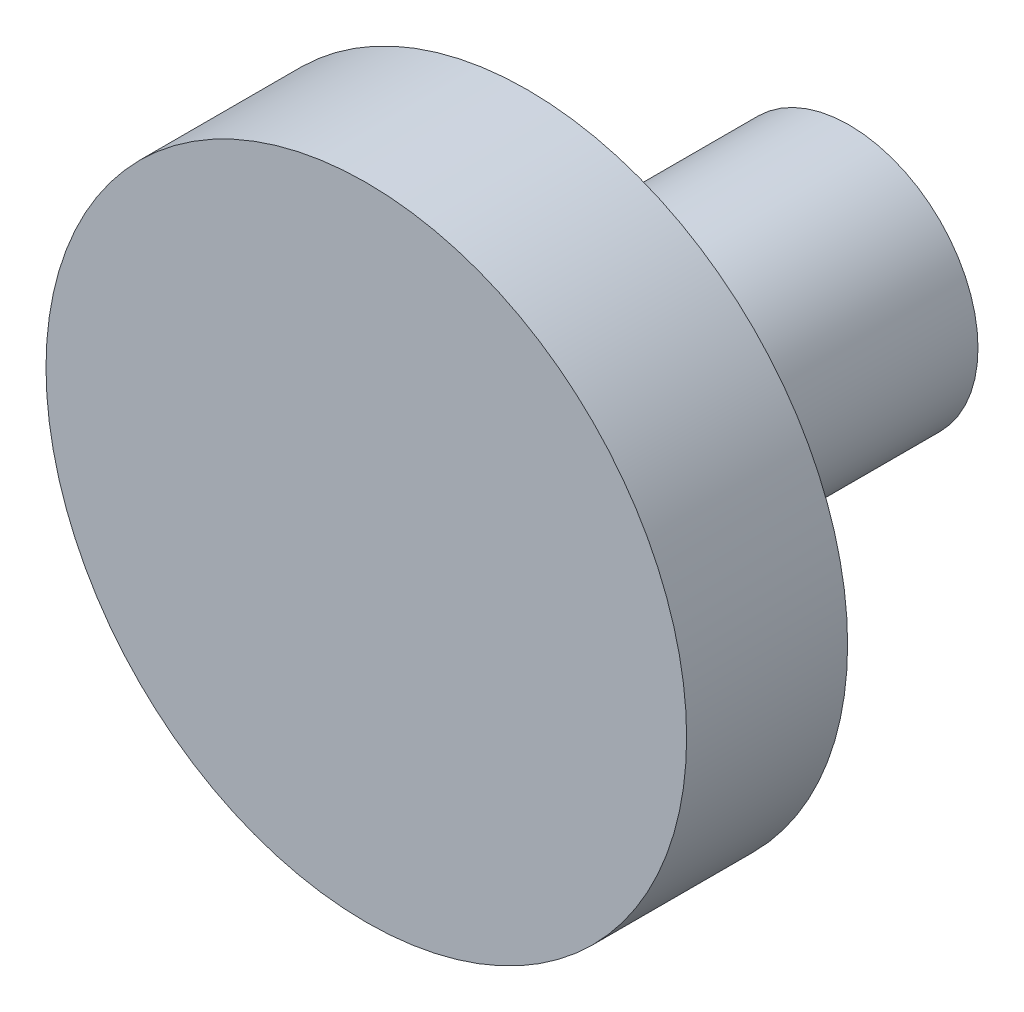
SolidWorks part; units mm, degrees
ref_plane "Front Plane" through (0, 0, 0) normal (0, 0, 1) x (1, 0, 0)
ref_plane "Top Plane" through (0, 0, 0) normal (0, 1, 0) x (1, 0, 0)
ref_plane "Right Plane" through (0, 0, 0) normal (1, 0, 0) x (0, 0, -1)
sketch "Sketch1" plane through (0, 0, 0) normal (0, 0, 1) x (1, 0, 0)
  circle A0 centre (0, 0) radius 9.95
extrude "Boss-Extrude1" add sketch "Sketch1" along normal blind 5
sketch "Sketch2" plane through (0, 0, 0) normal (0, 0, -1) x (-1, 0, 0)
  circle A0 centre (0, 0) radius 4
extrude "Boss-Extrude2" add sketch "Sketch2" along normal blind 10
